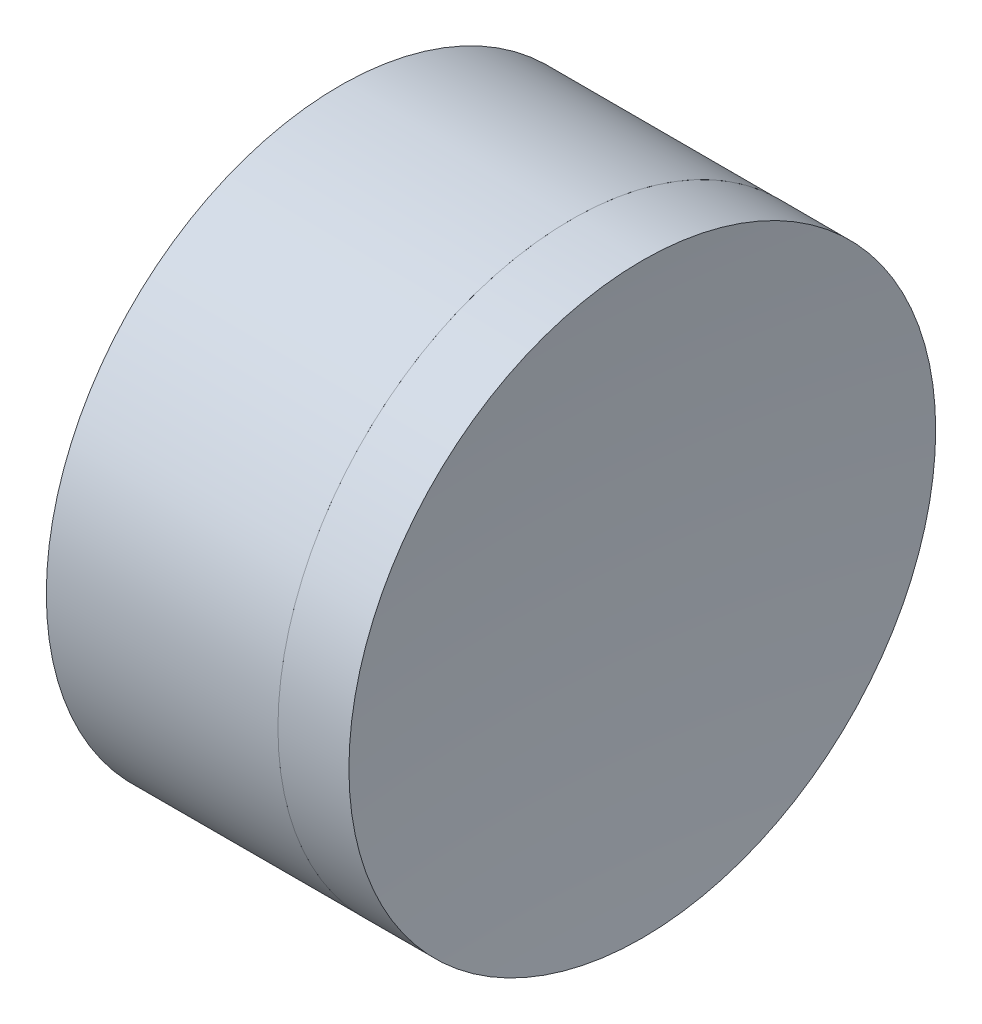
SolidWorks part; units mm, degrees
ref_plane "前视基准面" through (0, 0, 0) normal (0, 0, 1) x (1, 0, 0)
ref_plane "上视基准面" through (0, 0, 0) normal (0, 1, 0) x (1, 0, 0)
ref_plane "右视基准面" through (0, 0, 0) normal (1, 0, 0) x (0, 0, -1)
sketch "草图1" plane through (0, 0, 0) normal (0, 1, 0) x (1, 0, 0)
  line L0 (-0.8161, 0) -> (401.427, 0) construction
  line L1 (223.9432, 6.25) -> (228.8774, 6.25)
  line L4 (223.9432, -6.25) -> (228.8774, -6.25)
  arc A0 (223.9432, -6.25) -> (223.9432, 6.25) centre (200.3055, 0) ccw
  arc A1 (228.8774, 6.25) -> (228.8774, -6.25) centre (245.7255, 0) ccw
  point P6 (224.7555, 0)
  point P8 (227.7555, 0)
  dimension "D3" = 6.25
  dimension "D4" = 3
  dimension "D1" = 24.45
  dimension "D5" = 17.97
  dimension "D2" = 6.25
revolve "旋转1" add sketch "草图1" angle 360 about L0
sketch "草图2" plane through (0, 0, 0) normal (0, 1, 0) x (1, 0, 0)
  line L2 (223.9432, 0) -> (234.9944, 0) construction
  line L3 (223.9432, -6.25) -> (223.9432, 6.25) construction
  line L6 (228.8774, 6.25) -> (230.3894, 6.25)
  line L7 (228.8774, -6.25) -> (230.3894, -6.25)
  arc A2 (228.8774, 6.25) -> (228.8774, -6.25) centre (245.7255, 0) ccw construction
  arc A3 (228.8774, 6.25) -> (228.8774, -6.25) centre (245.7255, 0) ccw
  arc A4 (230.3894, 6.25) -> (230.3894, -6.25) centre (296.6955, 0) ccw
  point P8 (227.7555, 0)
  point P9 (230.0955, 0)
  dimension "D1" = 2.34
  dimension "D2" = 66.6
revolve "旋转3" add sketch "草图2" angle 360 about L2
